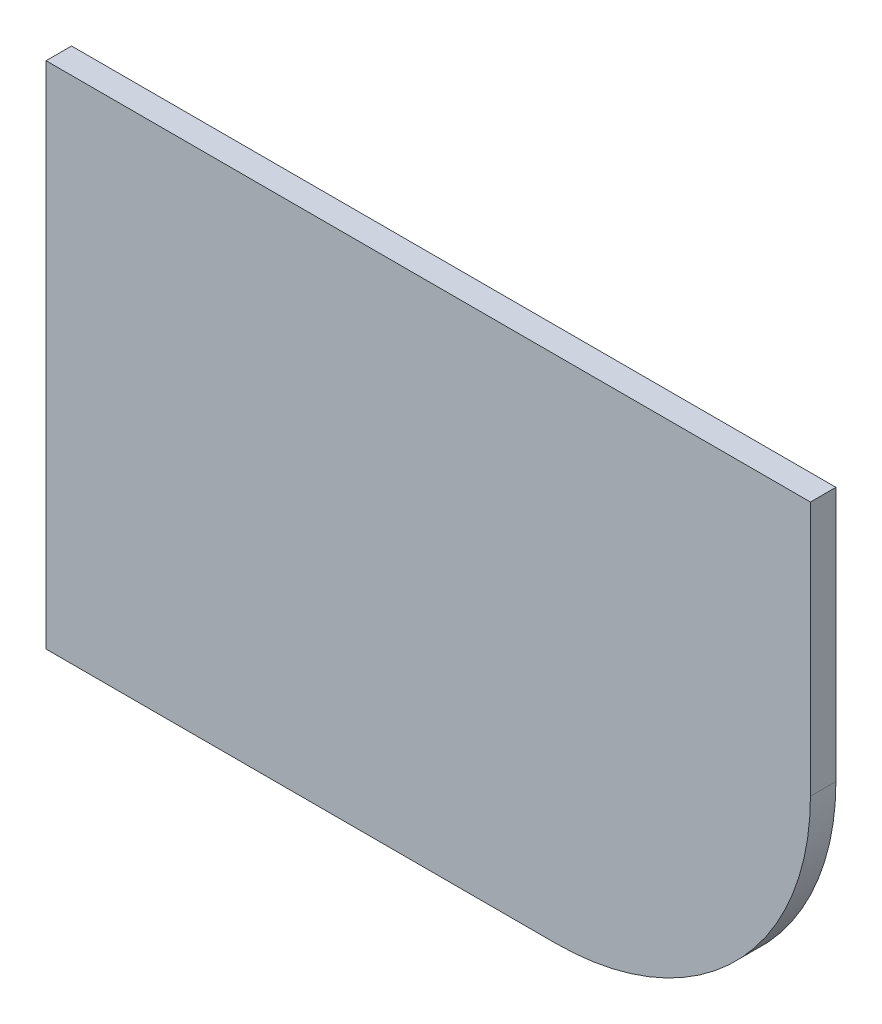
SolidWorks part; units mm, degrees
ref_plane "Front Plane" through (0, 0, 0) normal (0, 0, 1) x (1, 0, 0)
ref_plane "Top Plane" through (0, 0, 0) normal (0, 1, 0) x (1, 0, 0)
ref_plane "Right Plane" through (0, 0, 0) normal (1, 0, 0) x (0, 0, -1)
sketch "Sketch1" plane through (0, 0, 0) normal (0, 0, 1) x (1, 0, 0)
  line L0 (0, 200) -> (0, 0)
  line L1 (0, 200) -> (300, 200)
  line L2 (300, 200) -> (300, 100)
  line L3 (200, 0) -> (0, 0)
  arc A0 (300, 100) -> (200, 0) centre (200, 100) cw
  dimension "D1" = 300
  dimension "D3" = 100
  dimension "D2" = 200
extrude "Boss-Extrude1" add sketch "Sketch1" along normal mid plane 10
sketch "Sketch6" plane through (0, 0, -5) normal (0, 0, -1) x (-1, 0, 0)
  line L0 (0, 200) -> (0, 0) construction
  line L1 (0, 0) -> (-200, 0) construction
  circle A0 centre (-225, 140) radius 2.5
  circle A1 centre (-150, 90) radius 2.5
  circle A2 centre (-60, 140) radius 2.5
  circle A3 centre (-75, 40) radius 2.5
  dimension "D1" = 5
  dimension "D2" = 75
  dimension "D3" = 40
  dimension "D4" = 50
  dimension "D5" = 75
  dimension "D6" = 100
  dimension "D7" = 50
  dimension "D8" = 75
  dimension "D9" = 15
extrude "Cut-Extrude1" cut sketch "Sketch6" against normal blind 5
